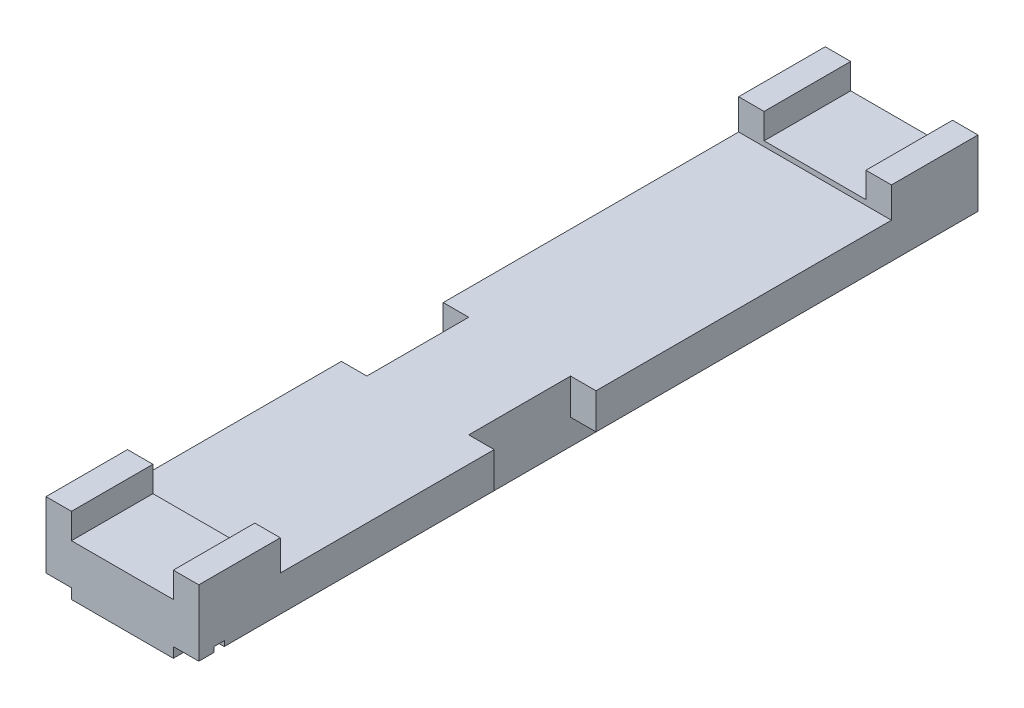
SolidWorks part; units mm, degrees
ref_plane "Front Plane" through (0, 0, 0) normal (0, 0, 1) x (1, 0, 0)
ref_plane "Top Plane" through (0, 0, 0) normal (0, 1, 0) x (1, 0, 0)
ref_plane "Right Plane" through (0, 0, 0) normal (1, 0, 0) x (0, 0, -1)
sketch "Sketch2" plane through (0, 0, 0) normal (0, 1, 0) x (1, 0, 0)
  line L0 (0, 0) -> (0, 15.3) construction
  line L2 (-1.5, 0) -> (1.5, 0)
  line L3 (-1.5, 0) -> (-1.5, 15.3)
  line L4 (-1.5, 15.3) -> (1.5, 15.3)
  line L5 (1.5, 0) -> (1.5, 15.3)
  dimension "D1" = 3
  dimension "D2" = 15.3
extrude "Boss-Extrude1" add sketch "Sketch2" along normal blind 1.8 contours L2 L5 L4 L3
sketch "Sketch3" plane through (1.5, 0, 0) normal (1, 0, 0) x (0, 0, -1)
  line L0 (0, 1.8) -> (15.3, 1.8) construction
  line L1 (1.6, 1.8) -> (13.6, 1.8)
  line L2 (1.6, 1.8) -> (1.6, 1.2)
  line L3 (1.6, 1.2) -> (13.6, 1.2)
  line L4 (13.6, 1.8) -> (13.6, 1.2)
  line L5 (0, 1.8) -> (0, 0) construction
  dimension "D1" = 1.6
  dimension "D2" = 12
  dimension "D3" = 0.6
extrude "Cut-Extrude1" cut sketch "Sketch3" against normal through all
sketch "Sketch4" plane through (1.5, 0, 0) normal (1, 0, 0) x (0, 0, -1)
  line L0 (0, 1.8) -> (0, 0) construction
  line L1 (0, 0.3) -> (2.3, 0.3)
  line L2 (0, 0.3) -> (0, 0)
  line L3 (0, 0) -> (2.3, 0)
  line L4 (2.3, 0.3) -> (2.3, 0)
  line L5 (0, 0) -> (15.3, 0) construction
  line L6 (13.6, 1.8) -> (15.3, 1.8) construction
  line L7 (15.3, 0) -> (12.3, 0)
  line L8 (15.3, 0) -> (15.3, 0.3)
  line L9 (15.3, 0.3) -> (12.3, 0.3)
  line L10 (12.3, 0) -> (12.3, 0.3)
  dimension "D1" = 2.3
  dimension "D2" = 10
  dimension "D3" = 1.5
extrude "Cut-Extrude2" cut sketch "Sketch4" against normal through all
sketch "Sketch5" plane through (0, 1.2, 0) normal (0, 1, 0) x (1, 0, 0)
  line L0 (0, 0) -> (0, 15.3) construction
  line L1 (-1.5, 0) -> (1.5, 0) construction
  line L2 (-1.5, 15.3) -> (1.5, 15.3) construction
  line L3 (-1.5, 1.6) -> (-1.5, 13.6) construction
  line L4 (-1.5, 7.8) -> (-1, 7.8)
  line L5 (-1.5, 7.8) -> (-1.5, 5.8)
  line L6 (-1.5, 5.8) -> (-1, 5.8)
  line L7 (-1, 7.8) -> (-1, 5.8)
  line L8 (1, 7.8) -> (1, 5.8)
  line L9 (1.5, 5.8) -> (1, 5.8)
  line L10 (1.5, 7.8) -> (1.5, 5.8)
  line L11 (1.5, 7.8) -> (1, 7.8)
  dimension "D1" = 5.8
  dimension "D2" = 2
  dimension "D3" = 2
extrude "Cut-Extrude3" cut sketch "Sketch5" against normal through all
sketch "Sketch8" plane through (0, 0, 0) normal (0, 0, 1) x (1, 0, 0)
  line L0 (0, 0) -> (0, 1.8) construction
  line L1 (-1.5, 0) -> (1.5, 0) construction
  line L2 (-1.5, 1.8) -> (1.5, 1.8) construction
  line L4 (-1, 1.8) -> (1, 1.8)
  line L5 (-1, 1.8) -> (-1, 1.3)
  line L6 (-1, 1.3) -> (1, 1.3)
  line L7 (1, 1.8) -> (1, 1.3)
  dimension "D1" = 0.5
  dimension "D2" = 2
extrude "Cut-Extrude5" cut sketch "Sketch8" against normal through all
sketch "Sketch9" plane through (0, 0, 0) normal (0, 0, 1) x (1, 0, 0)
  line L0 (0, 0) -> (0, 1.3) construction
  line L1 (-1, 1.3) -> (1, 1.3) construction
  line L2 (-1.5, 1.8) -> (-1, 1.8) construction
  line L3 (-1.5, 0) -> (-1, 0)
  line L4 (-1.5, 0) -> (-1.5, 0.5)
  line L5 (-1.5, 0.5) -> (-1, 0.5)
  line L6 (-1, 0) -> (-1, 0.5)
  line L7 (1, 0) -> (1, 0.5)
  line L8 (1.5, 0.5) -> (1, 0.5)
  line L9 (1.5, 0) -> (1.5, 0.5)
  line L10 (1.5, 0) -> (1, 0)
  dimension "D1" = 1.3
  dimension "D2" = 2
extrude "Cut-Extrude6" cut sketch "Sketch9" against normal through all
sketch "Sketch10" plane through (1.5, 0, 0) normal (1, 0, 0) x (0, 0, -1)
  line L0 (2.3, 0.3) -> (0, 0.3) construction
  line L1 (0.3, 0.6) -> (0.5, 0.6)
  line L2 (0.3, 0.6) -> (0.3, 0.3)
  line L3 (0.3, 0.3) -> (0.5, 0.3)
  line L4 (0.5, 0.6) -> (0.5, 0.3)
  line L5 (0, 1.8) -> (0, 0.5) construction
  dimension "D1" = 0.3
  dimension "D2" = 0.3
  dimension "D3" = 0.2
extrude "Cut-Extrude7" cut sketch "Sketch10" against normal through all
